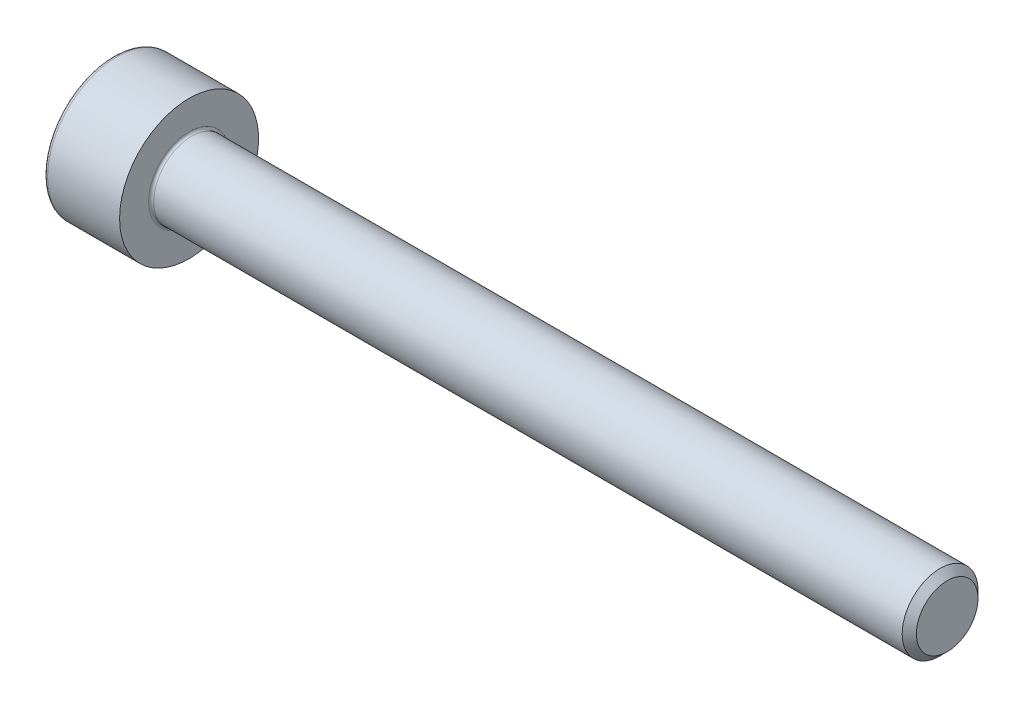
SolidWorks part; units mm, degrees
revolve "Base-Revolve" add sketch "BodySke"
sketch "BodySke" plane through (0, 0, 0) normal (0, 0, 1) x (1, 0, 0)
  line L0 (0, 0) -> (0, 2.75)
  line L1 (0, 2.75) -> (3, 2.75)
  line L2 (3, 2.75) -> (3, 1.5)
  line L3 (3, 1.5) -> (32.7195, 1.5)
  line L4 (33, 1.2195) -> (33, 0)
  line L5 (33, 0) -> (0, 0)
  line L6 (-31.75, 0) -> (127, 0) construction
  line L8 (33, 1.2195) -> (32.7195, 1.5)
  line L10 (33, -1.2195) -> (32.7195, -1.5) construction
  line L11 (3.5, 9.525) -> (3.5, 3.175) construction
  line L12 (15, 9.525) -> (15, 3.175) construction
  line L13 (-27, 9.525) -> (-27, 3.175) construction
  dimension "Head_ht" = 3
  dimension "Length" = 30
  dimension "Body_ch_ang" = 45
  dimension "Diameter" = 3
  dimension "Minor_dia" = 2.439
  dimension "Advance" = 0.5
  dimension "Thread_nom" = 18
  dimension "Thread_length" = 60
  dimension "Head_dia" = 5.5
cosmetic thread "ThreadCosmetic" [suppressed]
fillet "Fillet1" radius 0.1 1 edges at (3, 0, 1.5)
fillet "Fillet2" radius 0.15 1 edges at (0, 0, 2.75)
ref_plane "Plane1" through (0, 0, 0) normal (0, 0, 1) x (1, 0, 0)
ref_plane "Plane2" through (0, 0, 0) normal (0, 1, 0) x (1, 0, 0)
ref_plane "Plane3" through (0, 0, 0) normal (1, 0, 0) x (0, 0, -1)
sketch "Sketch2" plane through (0, 0, 0) normal (0, 0, 1) x (1, 0, 0)
  line L0 (0, 1.28) -> (1.3, 1.28)
  line L1 (1.3, 1.28) -> (2.039, 0)
  line L2 (-31.75, 0) -> (127, 0) construction
  line L3 (2.039, 0) -> (0, 0)
  line L4 (0, 0) -> (0, 1.28)
  line L6 (0, 0) -> (47.625, 0) construction
  dimension "D1" = 1.28
  dimension "D2" = 60
  dimension "Depth" = 1.3
revolve "Hex-PreBroach" cut sketch "Sketch2" angle 360 about L6
sketch "Sketch3" plane through (0, 0, 0) normal (-1, 0, 0) x (0, 0.5, 0.866)
  line L0 (0.739, 1.28) -> (-0.739, 1.28)
  line L1 (-0.739, 1.28) -> (-1.478, 0)
  line L2 (0.739, 1.28) -> (1.478, 0)
  line L3 (0.739, -1.28) -> (1.478, 0)
  line L4 (0.739, -1.28) -> (-0.739, -1.28)
  line L5 (-0.739, -1.28) -> (-1.478, 0)
  dimension "D1" = 1.28
  dimension "D2" = 1.28
  dimension "Hex_size" = 2.56
extrude "Hex" cut sketch "Sketch3" against normal blind 1.3
sketch "ThdSchSke" plane through (0, 0, 0) normal (0, 0, 1) x (1, 0, 0)
  line L0 (15, -1.2195) -> (14.8036, -1.5)
  line L1 (15, -1.2195) -> (15.1964, -1.5)
  line L2 (15.1964, -1.5) -> (15.1964, -1.875)
  line L3 (-3.175, 0) -> (5.1513, 0) construction
  line L4 (0, 2.6) -> (0, -2.6) construction
  line L5 (15.1964, -1.875) -> (14.8036, -1.875)
  line L6 (14.8036, -1.875) -> (14.8036, -1.5)
  dimension "Thread_minor" = 2.439
  dimension "Diameter" = 3
  dimension "Start" = 15
revolve "ThreadSchematic" [suppressed] cut sketch "ThdSchSke" angle 360 about L3
pattern_linear "ThdSchPat" [suppressed]
equation "\"D2@Sketch3\" = \"Hex_size@Sketch3\" / 2"
equation "\"D1@Sketch3\" = \"Hex_size@Sketch3\" / 2"
equation "\"D1@Sketch2\" = \"Hex_size@Sketch3\" / 2"
equation "\"Thread_minor@ThreadCosmetic\"  =  \"Minor_dia@BodySke\""
equation "\"Depth@Sketch2\" =  \"Key_eng@Hex\""
equation "\"Thread_length@ThreadCosmetic\" = ((sgn( (\"Length@BodySke\" - \"Advance@BodySke\" * 3.0) - \"Thread_nom@BodySke\" )-1)*( (\"Length@BodySke\" - \"Advance@BodySke\" * 3.0) - \"Thread_nom@BodySke\" ))/-2+ \"Thread_nom@BodySke\""
equation "\"Thread_minor@ThdSchSke\" = \"Minor_dia@BodySke\""
equation "\"Diameter@ThdSchSke\" = \"Diameter@BodySke\""
equation "\"Overcut@ThdSchSke\" = \"Diameter@BodySke\" * 1.25"
equation "\"Start@ThdSchSke\" = \"Head_ht@BodySke\" + \"Length@BodySke\" - \"Thread_length@ThreadCosmetic\"  '---Non-countersunk---"
equation "\"Num_threads@ThdSchPat\" = int( \"Thread_length@ThreadCosmetic\" / \"Advance@BodySke\" + 0.999 )  + 1"
equation "\"Advance@ThdSchPat\" = \"Thread_length@ThreadCosmetic\" /  (\"Num_threads@ThdSchPat\" - 1) 'relax it"
equation "\"Num_threads@ThdSchPat\" = \"Num_threads@ThdSchPat\" - sgn( \"Num_threads@ThdSchPat\" - 1) '---chamfered tips only---"
